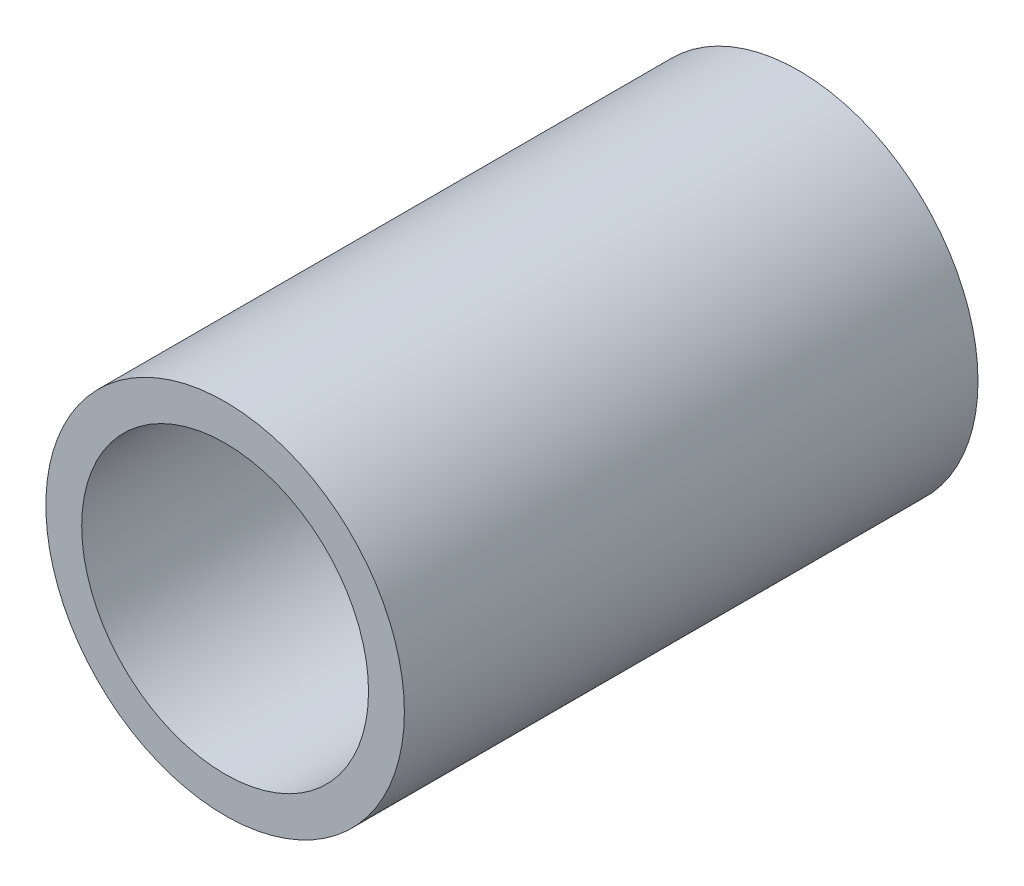
SolidWorks part; units mm, degrees
material "Plain Carbon Steel"
ref_plane "Front Plane" through (0, 0, 0) normal (0, 0, 1) x (1, 0, 0)
ref_plane "Top Plane" through (0, 0, 0) normal (0, 1, 0) x (1, 0, 0)
ref_plane "Right Plane" through (0, 0, 0) normal (1, 0, 0) x (0, 0, -1)
sketch "Sketch1" plane through (0, 0, 0) normal (0, 0, 1) x (1, 0, 0)
  circle A0 centre (0, 0) radius 15.875
  circle A1 centre (0, 0) radius 12.7
  dimension "D1" = 31.75
  dimension "D2" = 25.4
extrude "Boss-Extrude1" add sketch "Sketch1" along normal blind 50.8
